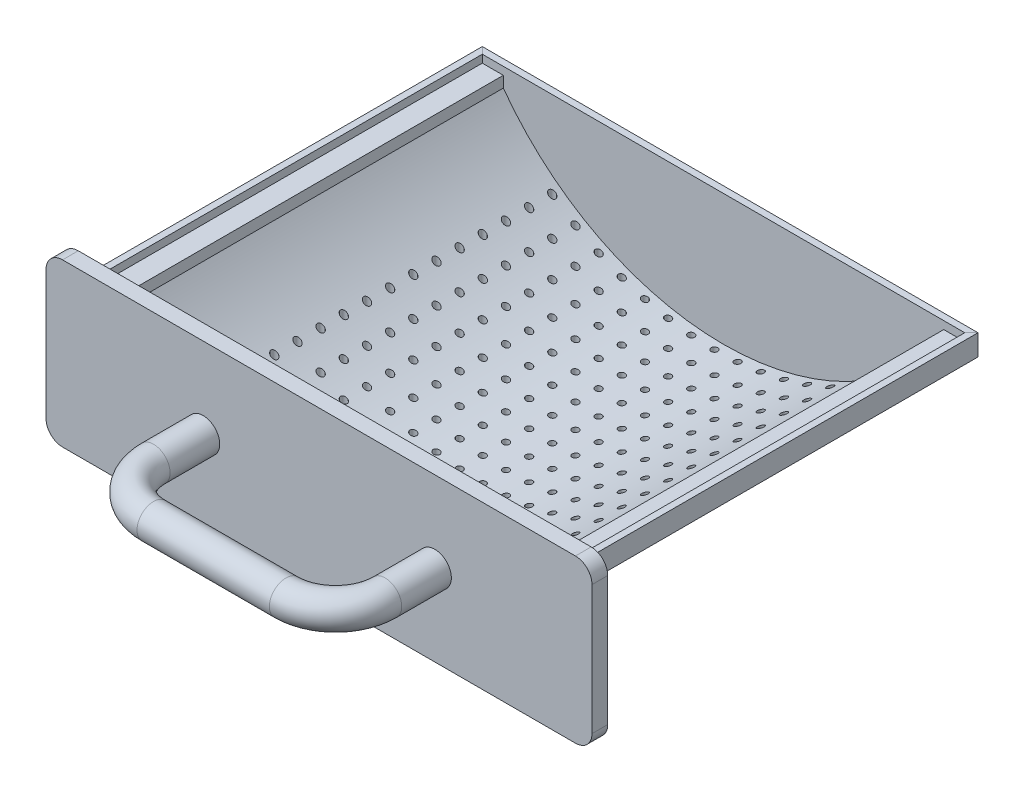
SolidWorks part; units mm, degrees
ref_plane "Plano frontal" through (0, 0, 0) normal (0, 0, 1) x (1, 0, 0)
ref_plane "Plano superior" through (0, 0, 0) normal (0, 1, 0) x (1, 0, 0)
ref_plane "Plano direito" through (0, 0, 0) normal (1, 0, 0) x (0, 0, -1)
sketch "Esboço1" plane through (0, 0, 0) normal (0, 0, 1) x (1, 0, 0)
  line L1 (77.5, -24.5) -> (-77.5, -24.5)
  line L2 (82.5, -19.5) -> (82.5, 19.5)
  line L3 (77.5, 24.5) -> (-77.5, 24.5)
  line L4 (-82.5, -19.5) -> (-82.5, 19.5)
  line L5 (82.5, -24.5) -> (-82.5, 24.5) construction
  line L6 (82.5, 24.5) -> (-82.5, -24.5) construction
  arc A0 (-77.5, 24.5) -> (-82.5, 19.5) centre (-77.5, 19.5) ccw
  arc A1 (-77.5, -24.5) -> (-82.5, -19.5) centre (-77.5, -19.5) cw
  arc A2 (77.5, -24.5) -> (82.5, -19.5) centre (77.5, -19.5) ccw
  arc A3 (82.5, 19.5) -> (77.5, 24.5) centre (77.5, 19.5) ccw
  point P0 (0, 0)
  dimension "D3" = 5
  dimension "D1" = 165
  dimension "D2" = 49
extrude "Ressalto-extrusão1" add sketch "Esboço1" along normal blind 4.75
sketch "Esboço2" plane through (0, 0, 4.75) normal (0, 0, 1) x (1, 0, 0)
  line L0 (0, 0) -> (0, 16.3689) construction
  circle A0 centre (-35, 0) radius 5
  dimension "D1" = 10
  dimension "D2" = 35
sketch "Esboço3" plane through (0, 0, 0) normal (0, 1, 0) x (1, 0, 0)
  line L0 (-35, -4.75) -> (-35, -19.75)
  line L1 (-20, -34.75) -> (20, -34.75)
  line L2 (35, -19.75) -> (35, -4.75)
  arc A0 (20, -34.75) -> (35, -19.75) centre (20, -19.75) ccw
  arc A1 (-35, -19.75) -> (-20, -34.75) centre (-20, -19.75) ccw
  point P10 (-35, -34.75)
  dimension "D2" = 15
  dimension "D1" = 30
  dimension "D3" = 70
  dimension "D4" = 30
sweep "Varredura1" add profiles "Esboço2" path "Esboço3"
sketch "Esboço4" plane through (0, 0, 0) normal (0, 0, -1) x (-1, 0, 0)
  line L0 (-74.9, 19.5) -> (-74.9, 13.15)
  line L1 (-74.9, 13.15) -> (-68.55, 13.15)
  line L2 (-68.55, 13.15) -> (-68.55, 15.15)
  line L3 (-68.55, 15.15) -> (-72.9, 15.15)
  line L4 (-72.9, 15.15) -> (-72.9, 19.5)
  line L5 (-72.9, 19.5) -> (-74.9, 19.5)
  line L6 (0, 0) -> (0, 11.0393) construction
  line L7 (-77.5, 24.5) -> (77.5, 24.5) construction
  line L8 (-74.9, 13.15) -> (-72.9, 15.15) construction
  dimension "D1" = 2
  dimension "D2" = 2
  dimension "D3" = 6.35
  dimension "D4" = 6.35
  dimension "D5" = 149.8
  dimension "D6" = 5
sketch "Esboço6" plane through (0, 0, 0) normal (0, 1, 0) x (1, 0, 0)
  line L0 (74.9, 0) -> (68.55, 0) construction
  line L1 (74, 0) -> (74, 118.6)
  line L2 (74, 118.6) -> (-74, 118.6)
  line L3 (-74, 118.6) -> (-74, 0)
  line L4 (0, 0) -> (0, 26.231) construction
  dimension "D1" = 148
  dimension "D2" = 118.6
  dimension "D3" = 118.6
  dimension "D4" = 148
sweep "Varredura2" add profiles "Esboço4" path "Esboço6"
sketch "Esboço7" plane through (0, 0, 0) normal (0, 0, -1) x (-1, 0, 0)
  line L0 (-68.55, 15.15) -> (-72.9, 15.15) construction
  line L1 (68.55, 15.15) -> (72.9, 15.15) construction
  line L2 (-68.55, 15.15) -> (-72.9, 15.15)
  line L3 (68.55, 15.15) -> (72.9, 15.15)
  line L4 (0, -24.5) -> (0, -22) construction
  line L5 (77.5, -24.5) -> (-77.5, -24.5) construction
  line L6 (-68.55, 13.15) -> (-68.55, 15.15) construction
  line L7 (68.55, 13.15) -> (68.55, 15.15) construction
  line L8 (-68.55, 13.15) -> (-68.55, 15.15)
  line L9 (68.55, 13.15) -> (68.55, 15.15)
  line L14 (66.55, 17.15) -> (72.9, 17.15)
  line L15 (66.55, 13.7984) -> (66.55, 17.15)
  line L16 (-66.55, 13.7984) -> (-66.55, 17.15)
  line L17 (-66.55, 17.15) -> (-72.9, 17.15)
  line L18 (-72.9, 17.15) -> (-72.9, 15.15)
  line L19 (72.9, 17.15) -> (72.9, 15.15)
  arc A0 (68.55, 13.15) -> (-68.55, 13.15) centre (0, 62.4186) cw
  arc A5 (66.55, 13.7984) -> (-66.55, 13.7984) centre (0, 62.4186) cw
  dimension "D1" = 2.5
  dimension "D2" = 2
sketch "Esboço8" plane through (0, 15.15, 0) normal (0, 1, 0) x (1, 0, 0)
  line L0 (72.9, 117.5) -> (-72.9, 117.5) construction
  line L1 (68.55, 113.15) -> (-68.55, 113.15)
  line L2 (68.55, 113.15) -> (68.55, 117.5)
  line L3 (68.55, 117.5) -> (-68.55, 117.5)
  line L4 (-68.55, 113.15) -> (-68.55, 117.5)
extrude "Corte-extrusão1" cut sketch "Esboço8" against normal through all
extrude "Ressalto-extrusão3" add sketch "Esboço7" along normal up to surface (119.5 mm away) contours L14 L19 L3 L9 A0 L8 L2 L18 L17 L16 A5 L15 up to face at (0, 16.325, -119.5)
sketch "Esboço10" plane through (0, 0, -119.5) normal (0, 0, -1) x (-1, 0, 0)
  line L0 (-66.0714, 13.15) -> (66.0714, 13.15) construction
  line L1 (-66.0714, 13.15) -> (66.0714, 13.15)
  arc A0 (-66.0714, 13.15) -> (66.0714, 13.15) centre (0, 62.4186) ccw construction
  arc A1 (-66.0714, 13.15) -> (66.0714, 13.15) centre (0, 62.4186) ccw
extrude "Ressalto-extrusão4" add sketch "Esboço10" against normal blind 2
sketch "Esboço11" plane through (0, 0, 0) normal (0, 1, 0) x (1, 0, 0)
  line L0 (0, 117.5) -> (0, 0) construction
  line L1 (-66.55, 117.5) -> (66.55, 117.5) construction
  line L2 (0, 58.75) -> (66.55, 58.75) construction
  line L3 (66.55, 117.5) -> (66.55, 0) construction
  circle A0 centre (0, 58.75) radius 1
  circle A1 centre (-7, 58.75) radius 1
  circle A2 centre (-14, 58.75) radius 1
  circle A3 centre (-21, 58.75) radius 1
  circle A4 centre (-28, 58.75) radius 1
  circle A5 centre (-35, 58.75) radius 1
  circle A6 centre (-42, 58.75) radius 1
  circle A7 centre (-49, 58.75) radius 1
  circle A8 centre (-56, 58.75) radius 1
  circle A9 centre (-63, 58.75) radius 1
  circle A10 centre (-7, 65.75) radius 1
  circle A11 centre (-14, 65.75) radius 1
  circle A12 centre (-21, 65.75) radius 1
  circle A13 centre (-28, 65.75) radius 1
  circle A14 centre (-35, 65.75) radius 1
  circle A15 centre (-42, 65.75) radius 1
  circle A16 centre (-49, 65.75) radius 1
  circle A17 centre (-56, 65.75) radius 1
  circle A18 centre (-63, 65.75) radius 1
  circle A19 centre (-7, 72.75) radius 1
  circle A20 centre (-14, 72.75) radius 1
  circle A21 centre (-21, 72.75) radius 1
  circle A22 centre (-28, 72.75) radius 1
  circle A23 centre (-35, 72.75) radius 1
  circle A24 centre (-42, 72.75) radius 1
  circle A25 centre (-49, 72.75) radius 1
  circle A26 centre (-56, 72.75) radius 1
  circle A27 centre (-63, 72.75) radius 1
  circle A28 centre (-7, 79.75) radius 1
  circle A29 centre (-14, 79.75) radius 1
  circle A30 centre (-21, 79.75) radius 1
  circle A31 centre (-28, 79.75) radius 1
  circle A32 centre (-35, 79.75) radius 1
  circle A33 centre (-42, 79.75) radius 1
  circle A34 centre (-49, 79.75) radius 1
  circle A35 centre (-56, 79.75) radius 1
  circle A36 centre (-63, 79.75) radius 1
  circle A37 centre (-7, 86.75) radius 1
  circle A38 centre (-14, 86.75) radius 1
  circle A39 centre (-21, 86.75) radius 1
  circle A40 centre (-28, 86.75) radius 1
  circle A41 centre (-35, 86.75) radius 1
  circle A42 centre (-42, 86.75) radius 1
  circle A43 centre (-49, 86.75) radius 1
  circle A44 centre (-56, 86.75) radius 1
  circle A45 centre (-63, 86.75) radius 1
  circle A46 centre (-7, 93.75) radius 1
  circle A47 centre (-14, 93.75) radius 1
  circle A48 centre (-21, 93.75) radius 1
  circle A49 centre (-28, 93.75) radius 1
  circle A50 centre (-35, 93.75) radius 1
  circle A51 centre (-42, 93.75) radius 1
  circle A52 centre (-49, 93.75) radius 1
  circle A53 centre (-56, 93.75) radius 1
  circle A54 centre (-63, 93.75) radius 1
  circle A55 centre (-7, 100.75) radius 1
  circle A56 centre (-14, 100.75) radius 1
  circle A57 centre (-21, 100.75) radius 1
  circle A58 centre (-28, 100.75) radius 1
  circle A59 centre (-35, 100.75) radius 1
  circle A60 centre (-42, 100.75) radius 1
  circle A61 centre (-49, 100.75) radius 1
  circle A62 centre (-56, 100.75) radius 1
  circle A63 centre (-63, 100.75) radius 1
  circle A64 centre (-7, 107.75) radius 1
  circle A65 centre (-14, 107.75) radius 1
  circle A66 centre (-21, 107.75) radius 1
  circle A67 centre (-28, 107.75) radius 1
  circle A68 centre (-35, 107.75) radius 1
  circle A69 centre (-42, 107.75) radius 1
  circle A70 centre (-49, 107.75) radius 1
  circle A71 centre (-56, 107.75) radius 1
  circle A72 centre (-63, 107.75) radius 1
  circle A73 centre (-7, 114.75) radius 1
  circle A74 centre (-14, 114.75) radius 1
  circle A75 centre (-21, 114.75) radius 1
  circle A76 centre (-28, 114.75) radius 1
  circle A77 centre (-35, 114.75) radius 1
  circle A78 centre (-42, 114.75) radius 1
  circle A79 centre (-49, 114.75) radius 1
  circle A80 centre (-56, 114.75) radius 1
  circle A81 centre (-63, 114.75) radius 1
  circle A82 centre (0, 65.75) radius 1
  circle A83 centre (0, 72.75) radius 1
  circle A84 centre (0, 79.75) radius 1
  circle A85 centre (0, 86.75) radius 1
  circle A86 centre (0, 93.75) radius 1
  circle A87 centre (0, 100.75) radius 1
  circle A88 centre (0, 107.75) radius 1
  circle A89 centre (0, 114.75) radius 1
  circle A90 centre (0, 2.75) radius 1
  circle A91 centre (-63, 2.75) radius 1
  circle A92 centre (-56, 2.75) radius 1
  circle A93 centre (-49, 2.75) radius 1
  circle A94 centre (-42, 2.75) radius 1
  circle A95 centre (-35, 2.75) radius 1
  circle A96 centre (-28, 2.75) radius 1
  circle A97 centre (-21, 2.75) radius 1
  circle A98 centre (-14, 2.75) radius 1
  circle A99 centre (-7, 2.75) radius 1
  circle A100 centre (0, 9.75) radius 1
  circle A101 centre (0, 16.75) radius 1
  circle A102 centre (0, 23.75) radius 1
  circle A103 centre (0, 30.75) radius 1
  circle A104 centre (0, 37.75) radius 1
  circle A105 centre (0, 44.75) radius 1
  circle A106 centre (0, 51.75) radius 1
  circle A107 centre (-63, 9.75) radius 1
  circle A108 centre (-56, 9.75) radius 1
  circle A109 centre (-49, 9.75) radius 1
  circle A110 centre (-42, 9.75) radius 1
  circle A111 centre (-35, 9.75) radius 1
  circle A112 centre (-28, 9.75) radius 1
  circle A113 centre (-21, 9.75) radius 1
  circle A114 centre (-14, 9.75) radius 1
  circle A115 centre (-7, 9.75) radius 1
  circle A116 centre (-63, 16.75) radius 1
  circle A117 centre (-56, 16.75) radius 1
  circle A118 centre (-49, 16.75) radius 1
  circle A119 centre (-42, 16.75) radius 1
  circle A120 centre (-35, 16.75) radius 1
  circle A121 centre (-28, 16.75) radius 1
  circle A122 centre (-21, 16.75) radius 1
  circle A123 centre (-14, 16.75) radius 1
  circle A124 centre (-7, 16.75) radius 1
  circle A125 centre (-63, 23.75) radius 1
  circle A126 centre (-56, 23.75) radius 1
  circle A127 centre (-49, 23.75) radius 1
  circle A128 centre (-42, 23.75) radius 1
  circle A129 centre (-35, 23.75) radius 1
  circle A130 centre (-28, 23.75) radius 1
  circle A131 centre (-21, 23.75) radius 1
  circle A132 centre (-14, 23.75) radius 1
  circle A133 centre (-7, 23.75) radius 1
  circle A134 centre (-63, 30.75) radius 1
  circle A135 centre (-56, 30.75) radius 1
  circle A136 centre (-49, 30.75) radius 1
  circle A137 centre (-42, 30.75) radius 1
  circle A138 centre (-35, 30.75) radius 1
  circle A139 centre (-28, 30.75) radius 1
  circle A140 centre (-21, 30.75) radius 1
  circle A141 centre (-14, 30.75) radius 1
  circle A142 centre (-7, 30.75) radius 1
  circle A143 centre (-63, 37.75) radius 1
  circle A144 centre (-56, 37.75) radius 1
  circle A145 centre (-49, 37.75) radius 1
  circle A146 centre (-42, 37.75) radius 1
  circle A147 centre (-35, 37.75) radius 1
  circle A148 centre (-28, 37.75) radius 1
  circle A149 centre (-21, 37.75) radius 1
  circle A150 centre (-14, 37.75) radius 1
  circle A151 centre (-7, 37.75) radius 1
  circle A152 centre (-63, 44.75) radius 1
  circle A153 centre (-56, 44.75) radius 1
  circle A154 centre (-49, 44.75) radius 1
  circle A155 centre (-42, 44.75) radius 1
  circle A156 centre (-35, 44.75) radius 1
  circle A157 centre (-28, 44.75) radius 1
  circle A158 centre (-21, 44.75) radius 1
  circle A159 centre (-14, 44.75) radius 1
  circle A160 centre (-7, 44.75) radius 1
  circle A161 centre (-63, 51.75) radius 1
  circle A162 centre (-56, 51.75) radius 1
  circle A163 centre (-49, 51.75) radius 1
  circle A164 centre (-42, 51.75) radius 1
  circle A165 centre (-35, 51.75) radius 1
  circle A166 centre (-28, 51.75) radius 1
  circle A167 centre (-21, 51.75) radius 1
  circle A168 centre (-14, 51.75) radius 1
  circle A169 centre (-7, 51.75) radius 1
  circle A170 centre (7, 51.75) radius 1
  circle A171 centre (14, 51.75) radius 1
  circle A172 centre (21, 51.75) radius 1
  circle A173 centre (28, 51.75) radius 1
  circle A174 centre (35, 51.75) radius 1
  circle A175 centre (42, 51.75) radius 1
  circle A176 centre (49, 51.75) radius 1
  circle A177 centre (56, 51.75) radius 1
  circle A178 centre (63, 51.75) radius 1
  circle A179 centre (7, 44.75) radius 1
  circle A180 centre (14, 44.75) radius 1
  circle A181 centre (21, 44.75) radius 1
  circle A182 centre (28, 44.75) radius 1
  circle A183 centre (35, 44.75) radius 1
  circle A184 centre (42, 44.75) radius 1
  circle A185 centre (49, 44.75) radius 1
  circle A186 centre (56, 44.75) radius 1
  circle A187 centre (63, 44.75) radius 1
  circle A188 centre (7, 37.75) radius 1
  circle A189 centre (14, 37.75) radius 1
  circle A190 centre (21, 37.75) radius 1
  circle A191 centre (28, 37.75) radius 1
  circle A192 centre (35, 37.75) radius 1
  circle A193 centre (42, 37.75) radius 1
  circle A194 centre (49, 37.75) radius 1
  circle A195 centre (56, 37.75) radius 1
  circle A196 centre (63, 37.75) radius 1
  circle A197 centre (7, 30.75) radius 1
  circle A198 centre (14, 30.75) radius 1
  circle A199 centre (21, 30.75) radius 1
  circle A200 centre (28, 30.75) radius 1
  circle A201 centre (35, 30.75) radius 1
  circle A202 centre (42, 30.75) radius 1
  circle A203 centre (49, 30.75) radius 1
  circle A204 centre (56, 30.75) radius 1
  circle A205 centre (63, 30.75) radius 1
  circle A206 centre (7, 23.75) radius 1
  circle A207 centre (14, 23.75) radius 1
  circle A208 centre (21, 23.75) radius 1
  circle A209 centre (28, 23.75) radius 1
  circle A210 centre (35, 23.75) radius 1
  circle A211 centre (42, 23.75) radius 1
  circle A212 centre (49, 23.75) radius 1
  circle A213 centre (56, 23.75) radius 1
  circle A214 centre (63, 23.75) radius 1
  circle A215 centre (7, 16.75) radius 1
  circle A216 centre (14, 16.75) radius 1
  circle A217 centre (21, 16.75) radius 1
  circle A218 centre (28, 16.75) radius 1
  circle A219 centre (35, 16.75) radius 1
  circle A220 centre (42, 16.75) radius 1
  circle A221 centre (49, 16.75) radius 1
  circle A222 centre (56, 16.75) radius 1
  circle A223 centre (63, 16.75) radius 1
  circle A224 centre (7, 9.75) radius 1
  circle A225 centre (14, 9.75) radius 1
  circle A226 centre (21, 9.75) radius 1
  circle A227 centre (28, 9.75) radius 1
  circle A228 centre (35, 9.75) radius 1
  circle A229 centre (42, 9.75) radius 1
  circle A230 centre (49, 9.75) radius 1
  circle A231 centre (56, 9.75) radius 1
  circle A232 centre (63, 9.75) radius 1
  circle A233 centre (7, 2.75) radius 1
  circle A234 centre (14, 2.75) radius 1
  circle A235 centre (21, 2.75) radius 1
  circle A236 centre (28, 2.75) radius 1
  circle A237 centre (35, 2.75) radius 1
  circle A238 centre (42, 2.75) radius 1
  circle A239 centre (49, 2.75) radius 1
  circle A240 centre (56, 2.75) radius 1
  circle A241 centre (63, 2.75) radius 1
  circle A242 centre (63, 114.75) radius 1
  circle A243 centre (56, 114.75) radius 1
  circle A244 centre (49, 114.75) radius 1
  circle A245 centre (42, 114.75) radius 1
  circle A246 centre (35, 114.75) radius 1
  circle A247 centre (28, 114.75) radius 1
  circle A248 centre (21, 114.75) radius 1
  circle A249 centre (14, 114.75) radius 1
  circle A250 centre (7, 114.75) radius 1
  circle A251 centre (63, 107.75) radius 1
  circle A252 centre (56, 107.75) radius 1
  circle A253 centre (49, 107.75) radius 1
  circle A254 centre (42, 107.75) radius 1
  circle A255 centre (35, 107.75) radius 1
  circle A256 centre (28, 107.75) radius 1
  circle A257 centre (21, 107.75) radius 1
  circle A258 centre (14, 107.75) radius 1
  circle A259 centre (7, 107.75) radius 1
  circle A260 centre (63, 100.75) radius 1
  circle A261 centre (56, 100.75) radius 1
  circle A262 centre (49, 100.75) radius 1
  circle A263 centre (42, 100.75) radius 1
  circle A264 centre (35, 100.75) radius 1
  circle A265 centre (28, 100.75) radius 1
  circle A266 centre (21, 100.75) radius 1
  circle A267 centre (14, 100.75) radius 1
  circle A268 centre (7, 100.75) radius 1
  circle A269 centre (63, 93.75) radius 1
  circle A270 centre (56, 93.75) radius 1
  circle A271 centre (49, 93.75) radius 1
  circle A272 centre (42, 93.75) radius 1
  circle A273 centre (35, 93.75) radius 1
  circle A274 centre (28, 93.75) radius 1
  circle A275 centre (21, 93.75) radius 1
  circle A276 centre (14, 93.75) radius 1
  circle A277 centre (7, 93.75) radius 1
  circle A278 centre (63, 86.75) radius 1
  circle A279 centre (56, 86.75) radius 1
  circle A280 centre (49, 86.75) radius 1
  circle A281 centre (42, 86.75) radius 1
  circle A282 centre (35, 86.75) radius 1
  circle A283 centre (28, 86.75) radius 1
  circle A284 centre (21, 86.75) radius 1
  circle A285 centre (14, 86.75) radius 1
  circle A286 centre (7, 86.75) radius 1
  circle A287 centre (63, 79.75) radius 1
  circle A288 centre (56, 79.75) radius 1
  circle A289 centre (49, 79.75) radius 1
  circle A290 centre (42, 79.75) radius 1
  circle A291 centre (35, 79.75) radius 1
  circle A292 centre (28, 79.75) radius 1
  circle A293 centre (21, 79.75) radius 1
  circle A294 centre (14, 79.75) radius 1
  circle A295 centre (7, 79.75) radius 1
  circle A296 centre (63, 72.75) radius 1
  circle A297 centre (56, 72.75) radius 1
  circle A298 centre (49, 72.75) radius 1
  circle A299 centre (42, 72.75) radius 1
  circle A300 centre (35, 72.75) radius 1
  circle A301 centre (28, 72.75) radius 1
  circle A302 centre (21, 72.75) radius 1
  circle A303 centre (14, 72.75) radius 1
  circle A304 centre (7, 72.75) radius 1
  circle A305 centre (63, 65.75) radius 1
  circle A306 centre (56, 65.75) radius 1
  circle A307 centre (49, 65.75) radius 1
  circle A308 centre (42, 65.75) radius 1
  circle A309 centre (35, 65.75) radius 1
  circle A310 centre (28, 65.75) radius 1
  circle A311 centre (21, 65.75) radius 1
  circle A312 centre (14, 65.75) radius 1
  circle A313 centre (7, 65.75) radius 1
  circle A314 centre (63, 58.75) radius 1
  circle A315 centre (56, 58.75) radius 1
  circle A316 centre (49, 58.75) radius 1
  circle A317 centre (42, 58.75) radius 1
  circle A318 centre (35, 58.75) radius 1
  circle A319 centre (28, 58.75) radius 1
  circle A320 centre (21, 58.75) radius 1
  circle A321 centre (14, 58.75) radius 1
  circle A322 centre (7, 58.75) radius 1
  dimension "D1" = 2
  dimension "D2" = 10
  dimension "D3" = 9
extrude "Corte-extrusão2" cut sketch "Esboço11" against normal through all
